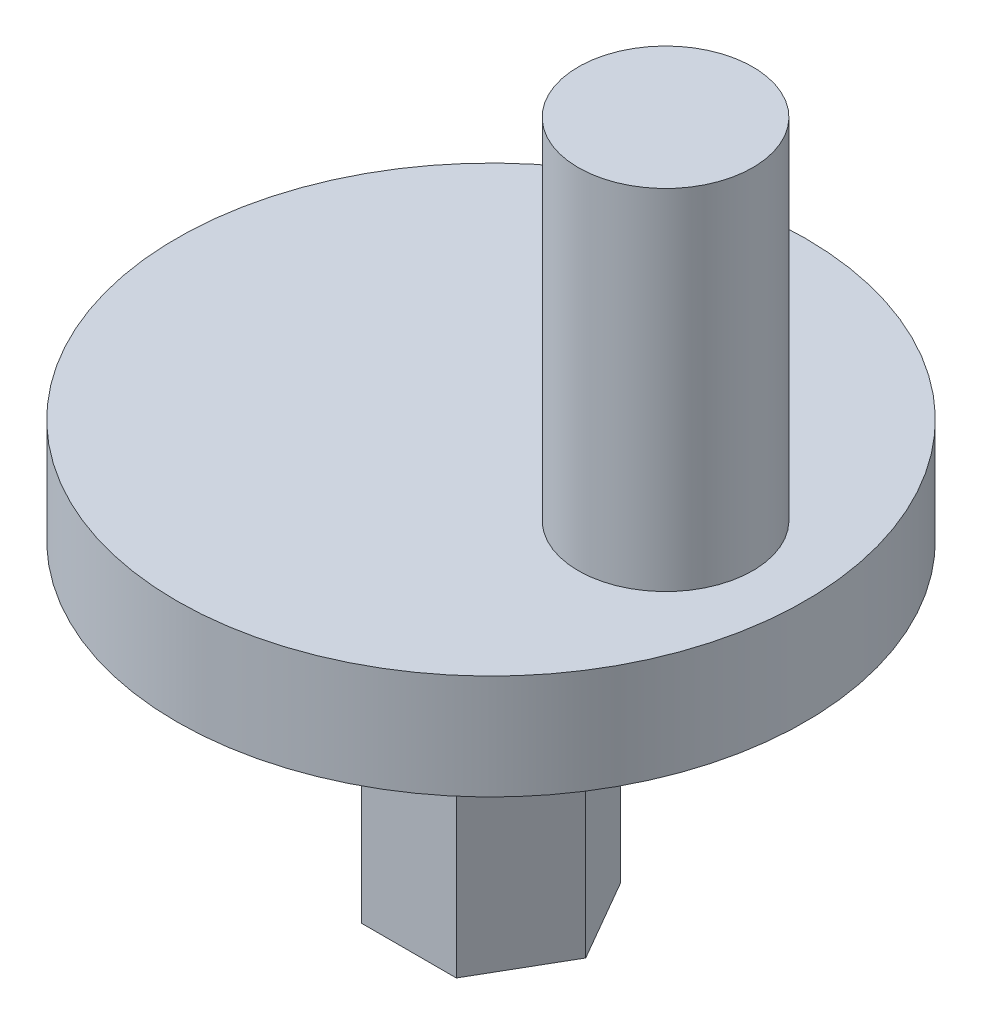
SolidWorks part; units mm, degrees
ref_plane "Front Plane" through (0, 0, 0) normal (0, 0, 1) x (1, 0, 0)
ref_plane "Top Plane" through (0, 0, 0) normal (0, 1, 0) x (1, 0, 0)
ref_plane "Right Plane" through (0, 0, 0) normal (1, 0, 0) x (0, 0, -1)
sketch "Sketch1" plane through (0, 0, 0) normal (0, 1, 0) x (1, 0, 0)
  circle A0 centre (0, 0) radius 9
  dimension "D1" = 18
extrude "Boss-Extrude1" add sketch "Sketch1" along normal blind 3
sketch "Sketch2" plane through (0, 3, 0) normal (0, 1, 0) x (1, 0, 0)
  circle A0 centre (5, 0) radius 2.5
  dimension "D2" = 5
  dimension "D1" = 5
extrude "Boss-Extrude2" add sketch "Sketch2" along normal blind 10
sketch "Sketch3" plane through (0, 0, 0) normal (0, -1, 0) x (1, 0, 0)
  line L1 (2.7135, 0) -> (1.3568, 2.35)
  line L2 (1.3568, 2.35) -> (-1.3568, 2.35)
  line L3 (-1.3568, 2.35) -> (-2.7135, 0)
  line L4 (-2.7135, 0) -> (-1.3568, -2.35)
  line L5 (-1.3568, -2.35) -> (1.3568, -2.35)
  line L6 (1.3568, -2.35) -> (2.7135, 0)
  circle A0 centre (0, 0) radius 2.35 construction
  dimension "D1" = 4.7
extrude "Boss-Extrude3" add sketch "Sketch3" along normal blind 9
